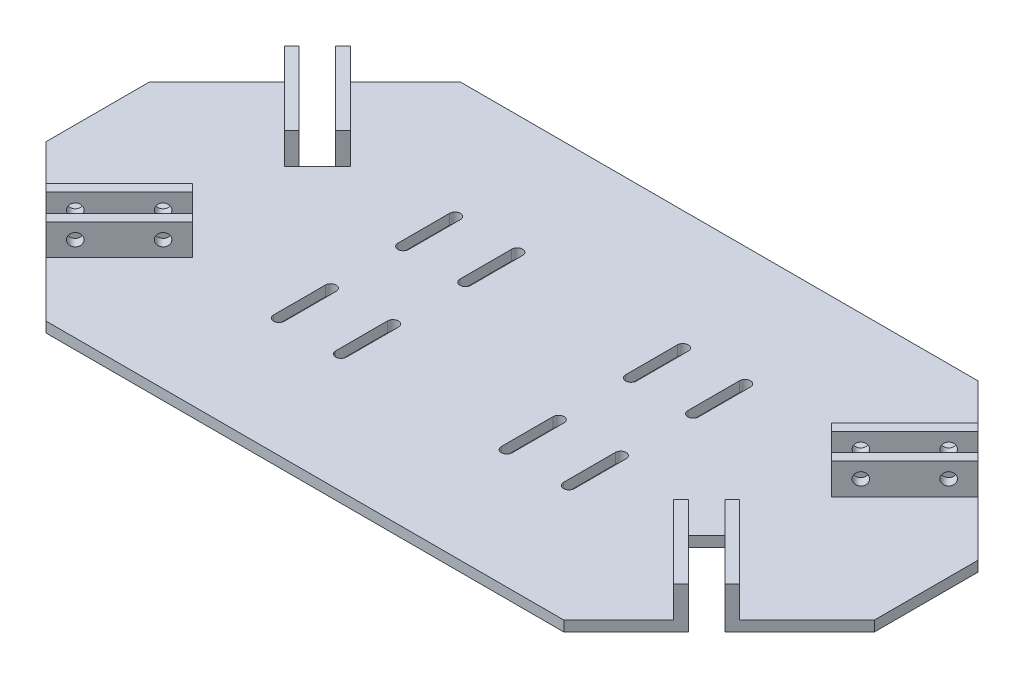
SolidWorks part; units mm, degrees
ref_plane "Plan de face" through (0, 0, 0) normal (0, 0, 1) x (1, 0, 0)
ref_plane "Plan de dessus" through (0, 0, 0) normal (0, 1, 0) x (1, 0, 0)
ref_plane "Plan de droite" through (0, 0, 0) normal (1, 0, 0) x (0, 0, -1)
sketch "Esquisse1" plane through (0, 0, 0) normal (0, 1, 0) x (1, 0, 0)
  line L1 (0, 0) -> (160, 0)
  line L2 (0, 0) -> (0, 80)
  line L3 (0, 80) -> (160, 80)
  line L4 (160, 0) -> (160, 80)
  dimension "D1" = 80
  dimension "D2" = 160
extrude "Boss.-Extru.1" add sketch "Esquisse1" along normal blind 2
sketch "Esquisse2" plane through (0, 2, 0) normal (0, 1, 0) x (1, 0, 0)
  line L0 (0, 50) -> (30, 80)
  line L1 (0, 80) -> (0, 0) construction
  line L2 (160, 80) -> (0, 80) construction
  line L3 (130, 80) -> (160, 50)
  line L4 (160, 0) -> (160, 80) construction
  line L5 (130, 0) -> (160, 30)
  line L6 (0, 0) -> (160, 0) construction
  line L7 (0, 30) -> (30, 0)
  line L8 (0, 80) -> (30, 80)
  line L9 (0, 30) -> (0, 0)
  line L10 (0, 0) -> (30, 0)
  line L11 (130, 0) -> (160, 0)
  line L12 (160, 0) -> (160, 30)
  line L13 (160, 50) -> (160, 80)
  line L14 (160, 80) -> (130, 80)
  line L15 (0, 80) -> (0, 50)
  dimension "D1" = 30
  dimension "D2" = 30
  dimension "D3" = 30
  dimension "D4" = 30
  dimension "D5" = 30
  dimension "D6" = 30
  dimension "D7" = 30
  dimension "D8" = 30
extrude "Enlèv. mat.-Extru.2" cut sketch "Esquisse2" against normal blind 2
sketch "Esquisse7" plane through (0, 2, 0) normal (0, 1, 0) x (1, 0, 0)
  line L0 (64, 23) -> (64, 33) construction
  line L1 (62.95, 23) -> (62.95, 33)
  line L2 (65.05, 23) -> (65.05, 33)
  line L3 (52, 23) -> (52, 33) construction
  line L4 (50.95, 23) -> (50.95, 33)
  line L5 (53.05, 23) -> (53.05, 33)
  line L6 (3.5692, 40) -> (183.2325, 40) construction
  line L7 (52, 47) -> (52, 57) construction
  line L8 (50.95, 47) -> (50.95, 57)
  line L9 (53.05, 47) -> (53.05, 57)
  line L10 (64, 47) -> (64, 57) construction
  line L11 (62.95, 47) -> (62.95, 57)
  line L12 (65.05, 47) -> (65.05, 57)
  line L13 (30, 0) -> (130, 0) construction
  line L14 (80, -22.0489) -> (80, 126.4706) construction
  line L15 (0, 50) -> (0, 30) construction
  line L16 (96, 47) -> (96, 57) construction
  line L17 (97.05, 47) -> (97.05, 57)
  line L18 (94.95, 47) -> (94.95, 57)
  line L19 (108, 47) -> (108, 57) construction
  line L20 (109.05, 47) -> (109.05, 57)
  line L21 (106.95, 47) -> (106.95, 57)
  line L22 (108, 23) -> (108, 33) construction
  line L23 (109.05, 23) -> (109.05, 33)
  line L24 (106.95, 23) -> (106.95, 33)
  line L25 (96, 23) -> (96, 33) construction
  line L26 (97.05, 23) -> (97.05, 33)
  line L27 (94.95, 23) -> (94.95, 33)
  arc A0 (62.95, 23) -> (65.05, 23) centre (64, 23) ccw
  arc A1 (65.05, 33) -> (62.95, 33) centre (64, 33) ccw
  arc A2 (50.95, 23) -> (53.05, 23) centre (52, 23) ccw
  arc A3 (53.05, 33) -> (50.95, 33) centre (52, 33) ccw
  arc A4 (50.95, 47) -> (53.05, 47) centre (52, 47) ccw
  arc A5 (53.05, 57) -> (50.95, 57) centre (52, 57) ccw
  arc A6 (62.95, 47) -> (65.05, 47) centre (64, 47) ccw
  arc A7 (65.05, 57) -> (62.95, 57) centre (64, 57) ccw
  arc A8 (97.05, 47) -> (94.95, 47) centre (96, 47) cw
  arc A9 (94.95, 57) -> (97.05, 57) centre (96, 57) cw
  arc A10 (109.05, 47) -> (106.95, 47) centre (108, 47) cw
  arc A11 (106.95, 57) -> (109.05, 57) centre (108, 57) cw
  arc A12 (109.05, 23) -> (106.95, 23) centre (108, 23) cw
  arc A13 (106.95, 33) -> (109.05, 33) centre (108, 33) cw
  arc A14 (97.05, 23) -> (94.95, 23) centre (96, 23) cw
  arc A15 (94.95, 33) -> (97.05, 33) centre (96, 33) cw
  point P2 (64, 28)
  point P7 (52, 28)
  point P18 (52, 52)
  point P23 (64, 52)
  point P38 (96, 52)
  point P45 (108, 52)
  point P52 (108, 28)
  point P59 (96, 28)
  dimension "D1" = 12
  dimension "D2" = 24
  dimension "D3" = 2.1
  dimension "D4" = 2.1
  dimension "D5" = 2.1
  dimension "D6" = 2.1
  dimension "D7" = 12
  dimension "D8" = 24
  dimension "D9" = 10
  dimension "D10" = 10
  dimension "D11" = 10
  dimension "D12" = 10
  dimension "D13" = 12
  dimension "D14" = 12
  dimension "D15" = 40
  dimension "D16" = 80
  dimension "D17" = 16
extrude "Enlèv. mat.-Extru.3" cut sketch "Esquisse7" against normal blind 2
sketch "Esquisse8" plane through (0, 2, 0) normal (0, 1, 0) x (1, 0, 0)
  line L0 (13.0294, 16.9706) -> (19.3934, 10.6066)
  line L1 (13.0294, 16.9706) -> (27.1716, 31.1127)
  line L2 (19.3934, 10.6066) -> (33.5355, 24.7487)
  line L3 (27.1716, 31.1127) -> (33.5355, 24.7487)
  line L4 (30, 0) -> (0, 30) construction
  line L5 (19.3934, 69.3934) -> (13.0294, 63.0294)
  line L6 (19.3934, 69.3934) -> (33.5355, 55.2513)
  line L7 (13.0294, 63.0294) -> (27.1716, 48.8873)
  line L8 (33.5355, 55.2513) -> (27.1716, 48.8873)
  line L9 (0, 50) -> (30, 80) construction
  line L10 (149.3934, 60.6066) -> (143.0294, 66.9706)
  line L11 (149.3934, 60.6066) -> (135.2513, 46.4645)
  line L12 (143.0294, 66.9706) -> (128.8873, 52.8284)
  line L13 (135.2513, 46.4645) -> (128.8873, 52.8284)
  line L14 (130, 80) -> (160, 50) construction
  line L15 (146.9706, 16.9706) -> (140.6066, 10.6066)
  line L16 (146.9706, 16.9706) -> (132.8284, 31.1127)
  line L17 (140.6066, 10.6066) -> (126.4645, 24.7487)
  line L18 (132.8284, 31.1127) -> (126.4645, 24.7487)
  line L19 (160, 30) -> (130, 0) construction
  dimension "D1" = 9
  dimension "D2" = 20
  dimension "D3" = 15
  dimension "D4" = 20
  dimension "D5" = 20
  dimension "D6" = 20
  dimension "D7" = 9
  dimension "D8" = 9
  dimension "D9" = 9
  dimension "D10" = 15
  dimension "D11" = 15
  dimension "D12" = 15
extrude "Boss.-Extru.2" add sketch "Esquisse8" along normal blind 6
sketch "Esquisse10" plane through (0, 8, 0) normal (0, 1, 0) x (1, 0, 0)
  line L0 (17.9792, 12.0208) -> (14.4437, 15.5563)
  line L1 (17.9792, 12.0208) -> (32.1213, 26.163)
  line L2 (14.4437, 15.5563) -> (28.5858, 29.6985)
  line L3 (32.1213, 26.163) -> (28.5858, 29.6985)
  line L4 (13.0294, 16.9706) -> (19.3934, 10.6066) construction
  line L6 (27.1716, 31.1127) -> (13.0294, 16.9706) construction
  line L7 (14.4437, 64.4437) -> (17.9792, 67.9792)
  line L8 (14.4437, 64.4437) -> (28.5858, 50.3015)
  line L9 (17.9792, 67.9792) -> (32.1213, 53.837)
  line L10 (28.5858, 50.3015) -> (32.1213, 53.837)
  line L11 (19.3934, 69.3934) -> (13.0294, 63.0294) construction
  line L13 (144.4437, 65.5563) -> (147.9792, 62.0208)
  line L14 (144.4437, 65.5563) -> (130.3015, 51.4142)
  line L15 (147.9792, 62.0208) -> (133.837, 47.8787)
  line L16 (130.3015, 51.4142) -> (133.837, 47.8787)
  line L17 (149.3934, 60.6066) -> (143.0294, 66.9706) construction
  line L18 (145.5563, 15.5563) -> (142.0208, 12.0208)
  line L19 (145.5563, 15.5563) -> (131.4142, 29.6985)
  line L20 (142.0208, 12.0208) -> (127.8787, 26.163)
  line L21 (131.4142, 29.6985) -> (127.8787, 26.163)
  line L22 (140.6066, 10.6066) -> (146.9706, 16.9706) construction
  line L24 (13.0294, 63.0294) -> (27.1716, 48.8873) construction
  line L26 (143.0294, 66.9706) -> (128.8873, 52.8284) construction
  line L27 (126.4645, 24.7487) -> (140.6066, 10.6066) construction
  dimension "D1" = 5
  dimension "D2" = 20
  dimension "D3" = 2
  dimension "D4" = 2
  dimension "D5" = 5
  dimension "D6" = 20
  dimension "D7" = 20
  dimension "D8" = 5
  dimension "D9" = 2
  dimension "D10" = 20
  dimension "D11" = 5
  dimension "D12" = 2
extrude "Enlèv. mat.-Extru.4" cut sketch "Esquisse10" against normal up to next
hole_wizard "Dégagement M21" positions "Esquisse12" profile "Esquisse14" size "M2" standard "ISO"
sketch "Esquisse12" plane through (4.3934, 0, 4.3934) normal (0.7071, 0, 0.7071) x (0.7071, 0, -0.7071)
  line L0 (21.2132, 8) -> (21.2132, 2) construction
  line L1 (41.2132, 8) -> (41.2132, 2) construction
  line L2 (21.2132, 8) -> (41.2132, 8) construction
  point P0 (25.2132, 5)
  point P2 (37.2132, 5)
  dimension "D1" = 4
  dimension "D2" = 4
  dimension "D3" = 3
  dimension "D4" = 3
sketch "Esquisse14" plane through (22.2218, 5, -13.435) normal (0, 1, 0) x (0.7071, 0, -0.7071)
  line L0 (0, 0) -> (0, 9.72)
  line L1 (0, 9.72) -> (1.2, 8.999)
  line L2 (1.2, 8.999) -> (1.2, 0)
  line L5 (1.2, 0) -> (0, 0)
  line L10 (0, 9.72) -> (-1.2, 8.999) construction
  line L11 (0, -6.35) -> (0, 107.95) construction
  dimension "Diamètre du perçage" = 2.4
  dimension "Profondeur du perçage" = 8.999
  dimension "Angle de pointe" = 118
hole_wizard "Dégagement M22" positions "Esquisse16" profile "Esquisse17" size "M2" standard "ISO"
sketch "Esquisse16" plane through (38.0294, 0, -38.0294) normal (-0.7071, 0, 0.7071) x (0.7071, 0, 0.7071)
  line L0 (-35.3553, 8) -> (-35.3553, 2) construction
  line L1 (-35.3553, 8) -> (-15.3553, 8) construction
  line L2 (-15.3553, 8) -> (-15.3553, 2) construction
  point P0 (-31.3553, 5)
  point P2 (-19.3553, 5)
  dimension "D1" = 4
  dimension "D2" = 3
  dimension "D3" = 4
  dimension "D4" = 3
sketch "Esquisse17" plane through (15.8579, 5, -60.201) normal (0, 1, 0) x (0.7071, 0, 0.7071)
  line L0 (0, 0) -> (0, 9.72)
  line L1 (0, 9.72) -> (1.2, 8.999)
  line L2 (1.2, 8.999) -> (1.2, 0)
  line L5 (1.2, 0) -> (0, 0)
  line L10 (0, 9.72) -> (-1.2, 8.999) construction
  line L11 (0, -6.35) -> (0, 107.95) construction
  dimension "Diamètre du perçage" = 2.4
  dimension "Profondeur du perçage" = 8.999
  dimension "Angle de pointe" = 118
hole_wizard "Dégagement M23" positions "Esquisse18" profile "Esquisse19" size "M2" standard "ISO"
sketch "Esquisse18" plane through (75.6066, 0, -75.6066) normal (-0.7071, 0, 0.7071) x (0.7071, 0, 0.7071)
  line L0 (71.9239, 8) -> (71.9239, 2) construction
  line L1 (71.9239, 8) -> (91.9239, 8) construction
  line L2 (91.9239, 8) -> (91.9239, 2) construction
  point P0 (75.9239, 5)
  point P2 (87.9239, 5)
  dimension "D1" = 4
  dimension "D2" = 3
  dimension "D3" = 4
  dimension "D4" = 3
sketch "Esquisse19" plane through (129.2929, 5, -21.9203) normal (0, 1, 0) x (0.7071, 0, 0.7071)
  line L0 (0, 0) -> (0, 9.72)
  line L1 (0, 9.72) -> (1.2, 8.999)
  line L2 (1.2, 8.999) -> (1.2, 0)
  line L5 (1.2, 0) -> (0, 0)
  line L10 (0, 9.72) -> (-1.2, 8.999) construction
  line L11 (0, -6.35) -> (0, 107.95) construction
  dimension "Diamètre du perçage" = 2.4
  dimension "Profondeur du perçage" = 8.999
  dimension "Angle de pointe" = 118
hole_wizard "Dégagement M24" positions "Esquisse20" profile "Esquisse21" size "M2" standard "ISO"
sketch "Esquisse20" plane through (38.0294, 0, 38.0294) normal (-0.7071, 0, -0.7071) x (-0.7071, 0, 0.7071)
  line L0 (-148.4924, 8) -> (-148.4924, 2) construction
  line L1 (-128.4924, 8) -> (-128.4924, 2) construction
  line L2 (-148.4924, 8) -> (-128.4924, 8) construction
  point P0 (-144.4924, 5)
  point P2 (-132.4924, 5)
  dimension "D1" = 4
  dimension "D2" = 4
  dimension "D3" = 3
  dimension "D4" = 3
sketch "Esquisse21" plane through (140.201, 5, -64.1421) normal (0, 1, 0) x (-0.7071, 0, 0.7071)
  line L0 (0, 0) -> (0, 9.72)
  line L1 (0, 9.72) -> (1.2, 8.999)
  line L2 (1.2, 8.999) -> (1.2, 0)
  line L5 (1.2, 0) -> (0, 0)
  line L10 (0, 9.72) -> (-1.2, 8.999) construction
  line L11 (0, -6.35) -> (0, 107.95) construction
  dimension "Diamètre du perçage" = 2.4
  dimension "Profondeur du perçage" = 8.999
  dimension "Angle de pointe" = 118
